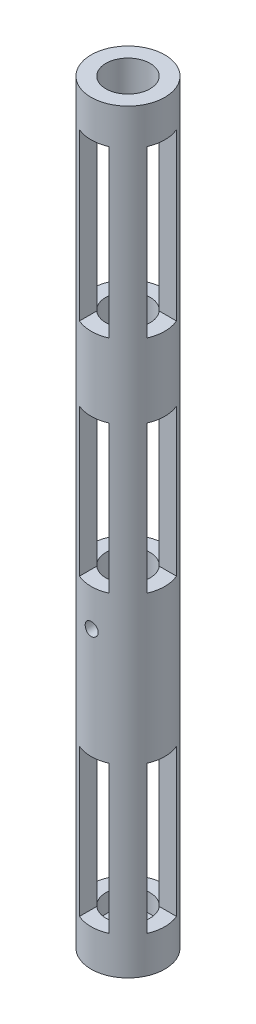
SolidWorks part; units mm, degrees
ref_plane "Front Plane" through (0, 0, 0) normal (0, 0, 1) x (1, 0, 0)
ref_plane "Top Plane" through (0, 0, 0) normal (0, 1, 0) x (1, 0, 0)
ref_plane "Right Plane" through (0, 0, 0) normal (1, 0, 0) x (0, 0, -1)
sketch "Sketch1" plane through (0, 0, 0) normal (0, 1, 0) x (1, 0, 0)
  circle A0 centre (0, 0) radius 7.62
  circle A1 centre (0, 0) radius 12.7
  dimension "D1" = 15.24
  dimension "D2" = 5.08
extrude "Boss-Extrude1" add sketch "Sketch1" along normal blind 260.35
sketch "Sketch2" plane through (0, 0, 0) normal (0, -1, 0) x (1, 0, 0)
  circle A0 centre (0, 0) radius 7.62
  dimension "D1" = 15.24
extrude "Boss-Extrude2" add sketch "Sketch2" against normal blind 6.35
ref_plane "Plane1" through (0, 0, 16.51) normal (0, 0, 1) x (1, 0, 0)
sketch "Sketch3" plane through (0, 0, 16.51) normal (0, 0, 1) x (1, 0, 0)
  line L0 (-12.7, 0) -> (12.7, 0) construction
  line L1 (0, 101.6) -> (0, 0) construction
  circle A0 centre (0, 101.6) radius 2.2479
  dimension "D1" = 4.4958
  dimension "D2" = 101.6
extrude "Cut-Extrude1" cut sketch "Sketch3" against normal through all and the other way through all contours A0
sketch "Sketch5" plane through (0, 0, 0) normal (1, 0, 0) x (0, 0, -1)
  line L0 (13.97, 0) -> (-13.97, 0) construction
  line L1 (5.08, 12.7) -> (-5.08, 12.7)
  line L2 (5.08, 12.7) -> (5.08, 247.65)
  line L3 (5.08, 247.65) -> (-5.08, 247.65)
  line L4 (-5.08, 12.7) -> (-5.08, 247.65)
  line L5 (12.7, 260.35) -> (-12.7, 260.35) construction
  line L6 (0, 0) -> (0, 12.7) construction
  line L7 (-5.08, 114.3) -> (7.62, 114.3)
  line L8 (-5.08, 63.5) -> (7.62, 63.5)
  line L9 (-5.08, 165.1) -> (5.08, 165.1)
  line L10 (-5.08, 190.5) -> (5.08, 190.5)
  dimension "D1" = 12.7
  dimension "D2" = 12.7
  dimension "D3" = 10.16
  dimension "D4" = 12.7
  dimension "D5" = 12.7
  dimension "D6" = 50.8
  dimension "D7" = 50.8
  dimension "D8" = 25.4
  dimension "D9" = 50.8
extrude "Cut-Extrude5" cut sketch "Sketch5" against normal through all both and the other way through all contours L8 L4 L1 L2 | L9 L4 L7 L2 | L4 L10 L2 L3
sketch "Sketch8" plane through (0, 0, 0) normal (0, 0, 1) x (1, 0, 0)
  line L0 (-12.7, 0) -> (12.7, 0) construction
  line L1 (5.08, 12.7) -> (-5.08, 12.7)
  line L2 (5.08, 12.7) -> (5.08, 247.65)
  line L3 (5.08, 247.65) -> (-5.08, 247.65)
  line L4 (-5.08, 12.7) -> (-5.08, 247.65)
  line L5 (12.7, 260.35) -> (-12.7, 260.35) construction
  line L6 (0, 12.7) -> (0, 0) construction
  line L7 (5.08, 63.5) -> (-5.08, 63.5)
  line L8 (5.08, 114.3) -> (-5.08, 114.3)
  line L9 (5.08, 165.1) -> (-5.08, 165.1)
  line L10 (5.08, 190.5) -> (-5.08, 190.5)
  dimension "D1" = 12.7
  dimension "D2" = 10.16
  dimension "D3" = 12.7
  dimension "D4" = 50.8
  dimension "D5" = 50.8
  dimension "D6" = 25.4
  dimension "D7" = 50.8
extrude "Cut-Extrude6" cut sketch "Sketch8" against normal through all both and the other way through all contours L2 L7 L4 L1 | L2 L9 L4 L8 | L10 L2 L3 L4
sketch "Sketch7" plane through (0, 6.35, 0) normal (0, 1, 0) x (1, 0, 0)
  circle A0 centre (0, 0) radius 3.81
  dimension "D1" = 7.62
extrude "Cut-Extrude4" cut sketch "Sketch7" against normal through all
